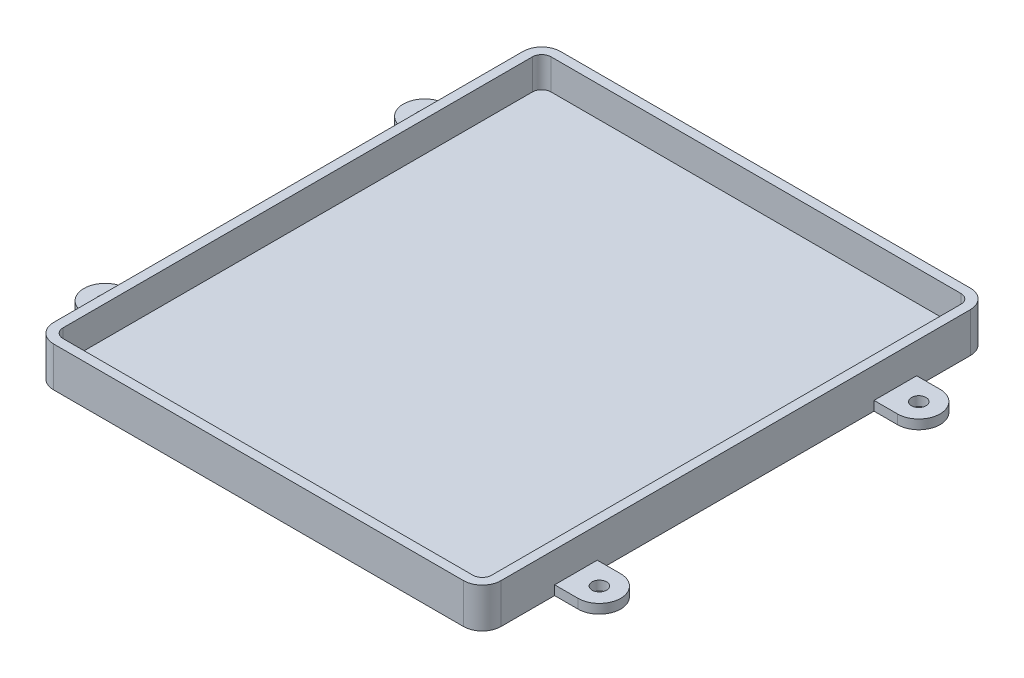
SolidWorks part; units mm, degrees
ref_plane "Alzado" through (0, 0, 0) normal (0, 0, 1) x (1, 0, 0)
ref_plane "Planta" through (0, 0, 0) normal (0, 1, 0) x (1, 0, 0)
ref_plane "Vista lateral" through (0, 0, 0) normal (1, 0, 0) x (0, 0, -1)
sketch "Croquis1" plane through (0, 0, 0) normal (0, 1, 0) x (1, 0, 0)
  line L0 (-47.75, 50.1) -> (-47.75, -50.1)
  line L1 (-43.75, 52.1) -> (43.75, 52.1)
  line L2 (-45.75, 50.1) -> (-45.75, -50.1)
  line L3 (-43.75, -52.1) -> (43.75, -52.1)
  line L4 (45.75, 50.1) -> (45.75, -50.1)
  line L5 (-45.75, 52.1) -> (45.75, -52.1) construction
  line L6 (-45.75, -52.1) -> (45.75, 52.1) construction
  line L7 (-43.75, -54.1) -> (43.75, -54.1)
  line L8 (47.75, 50.1) -> (47.75, -50.1)
  line L9 (-43.75, 54.1) -> (43.75, 54.1)
  arc A0 (-45.75, -50.1) -> (-43.75, -52.1) centre (-43.75, -50.1) ccw
  arc A1 (43.75, -52.1) -> (45.75, -50.1) centre (43.75, -50.1) ccw
  arc A2 (43.75, 52.1) -> (45.75, 50.1) centre (43.75, 50.1) cw
  arc A3 (-43.75, 52.1) -> (-45.75, 50.1) centre (-43.75, 50.1) ccw
  arc A4 (-47.75, -50.1) -> (-43.75, -54.1) centre (-43.75, -50.1) ccw
  arc A5 (43.75, -54.1) -> (47.75, -50.1) centre (43.75, -50.1) ccw
  arc A6 (43.75, 54.1) -> (47.75, 50.1) centre (43.75, 50.1) cw
  arc A7 (-43.75, 54.1) -> (-47.75, 50.1) centre (-43.75, 50.1) ccw
  point P0 (0, 0)
  dimension "D3" = 2
  dimension "D1" = 91.5
  dimension "D2" = 104.2
  dimension "D4" = 2
extrude "Saliente-Extruir1" add sketch "Croquis1" along normal blind 8.5
sketch "Croquis2" plane through (0, 0, 0) normal (0, 1, 0) x (1, 0, 0)
  line L4 (43.75, 54.1) -> (-43.75, 54.1)
  line L5 (47.75, -50.1) -> (47.75, 50.1)
  line L6 (-43.75, -54.1) -> (43.75, -54.1)
  line L7 (-47.75, 50.1) -> (-47.75, -50.1)
  line L8 (43.75, 54.1) -> (-43.75, 54.1)
  line L9 (47.75, -50.1) -> (47.75, 50.1)
  line L10 (-43.75, -54.1) -> (43.75, -54.1)
  line L11 (-47.75, 50.1) -> (-47.75, -50.1)
  arc A4 (-43.75, 54.1) -> (-47.75, 50.1) centre (-43.75, 50.1) ccw
  arc A5 (47.75, 50.1) -> (43.75, 54.1) centre (43.75, 50.1) ccw
  arc A6 (43.75, -54.1) -> (47.75, -50.1) centre (43.75, -50.1) ccw
  arc A7 (-47.75, -50.1) -> (-43.75, -54.1) centre (-43.75, -50.1) ccw
  arc A8 (-43.75, 54.1) -> (-47.75, 50.1) centre (-43.75, 50.1) ccw
  arc A9 (47.75, 50.1) -> (43.75, 54.1) centre (43.75, 50.1) ccw
  arc A10 (43.75, -54.1) -> (47.75, -50.1) centre (43.75, -50.1) ccw
  arc A11 (-47.75, -50.1) -> (-43.75, -54.1) centre (-43.75, -50.1) ccw
  dimension "D1" = 0
extrude "Saliente-Extruir2" add sketch "Croquis2" along normal blind 2
sketch "Croquis3" plane through (0, 0, 0) normal (0, 1, 0) x (1, 0, 0)
  line L0 (-52.75, 34.1) -> (0, 34.1) construction
  line L1 (0, 34.1) -> (0, 0) construction
  line L2 (0, 0) -> (12.3292, 0) construction
  line L3 (-52.75, 38.65) -> (-47.75, 38.65)
  line L4 (-47.75, 50.1) -> (-47.75, -50.1)
  line L5 (-43.75, -54.1) -> (43.75, -54.1)
  line L6 (47.75, -50.1) -> (47.75, 50.1)
  line L7 (43.75, 54.1) -> (-43.75, 54.1)
  line L8 (-47.75, 50.1) -> (-47.75, 38.65)
  line L9 (-43.75, -54.1) -> (43.75, -54.1)
  line L10 (47.75, -50.1) -> (47.75, -38.65)
  line L11 (43.75, 54.1) -> (-43.75, 54.1)
  line L12 (-52.75, 29.55) -> (-47.75, 29.55)
  line L13 (-47.75, 29.55) -> (-47.75, -29.55)
  line L14 (52.75, 38.65) -> (47.75, 38.65)
  line L15 (52.75, 29.55) -> (47.75, 29.55)
  line L16 (47.75, 38.65) -> (47.75, 50.1)
  line L17 (52.75, -38.65) -> (47.75, -38.65)
  line L18 (52.75, -29.55) -> (47.75, -29.55)
  line L19 (-52.75, -38.65) -> (-47.75, -38.65)
  line L20 (-52.75, -29.55) -> (-47.75, -29.55)
  line L21 (-47.75, -38.65) -> (-47.75, -50.1)
  line L22 (47.75, -29.55) -> (47.75, 29.55)
  circle A0 centre (-52.75, 34.1) radius 1.55
  arc A1 (-52.75, 38.65) -> (-52.75, 29.55) centre (-52.75, 34.1) ccw
  circle A2 centre (-52.75, 34.1) radius 4.55 construction
  circle A3 centre (52.75, 34.1) radius 1.55
  arc A4 (-43.75, 54.1) -> (-47.75, 50.1) centre (-43.75, 50.1) ccw
  arc A5 (-47.75, -50.1) -> (-43.75, -54.1) centre (-43.75, -50.1) ccw
  arc A6 (43.75, -54.1) -> (47.75, -50.1) centre (43.75, -50.1) ccw
  arc A7 (47.75, 50.1) -> (43.75, 54.1) centre (43.75, 50.1) ccw
  arc A8 (-43.75, 54.1) -> (-47.75, 50.1) centre (-43.75, 50.1) ccw
  arc A9 (-47.75, -50.1) -> (-43.75, -54.1) centre (-43.75, -50.1) ccw
  arc A10 (43.75, -54.1) -> (47.75, -50.1) centre (43.75, -50.1) ccw
  arc A11 (47.75, 50.1) -> (43.75, 54.1) centre (43.75, 50.1) ccw
  arc A12 (52.75, 38.65) -> (52.75, 29.55) centre (52.75, 34.1) cw
  circle A13 centre (52.75, -34.1) radius 1.55
  arc A14 (52.75, -38.65) -> (52.75, -29.55) centre (52.75, -34.1) ccw
  circle A15 centre (-52.75, -34.1) radius 1.55
  arc A16 (-52.75, -38.65) -> (-52.75, -29.55) centre (-52.75, -34.1) cw
  dimension "D2" = 3.1
  dimension "D3" = 5
  dimension "D5" = 20
  dimension "D1" = 0
  dimension "D4" = 3
extrude "Saliente-Extruir3" add sketch "Croquis3" along normal blind 2
